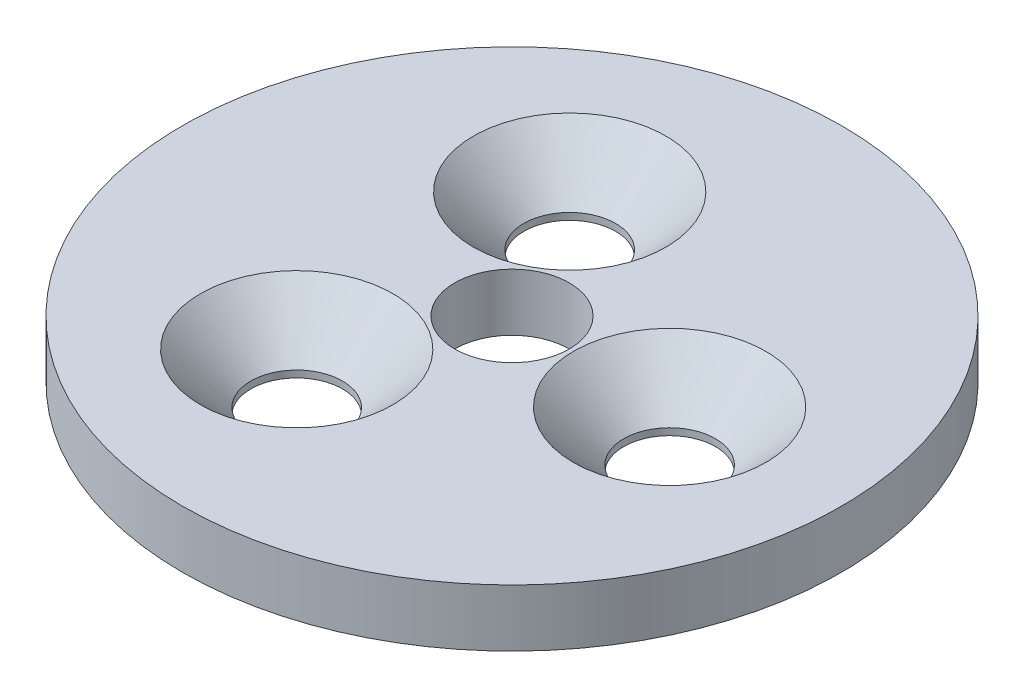
SolidWorks part; units mm, degrees
ref_plane "Ebene vorne" through (0, 0, 0) normal (0, 0, 1) x (1, 0, 0)
ref_plane "Ebene oben" through (0, 0, 0) normal (0, 1, 0) x (1, 0, 0)
ref_plane "Ebene rechts" through (0, 0, 0) normal (1, 0, 0) x (0, 0, -1)
sketch "Skizze1" plane through (0, 0, 0) normal (0, 1, 0) x (1, 0, 0)
  circle A0 centre (0, 0) radius 11.5
  dimension "D1" = 23
extrude "Aufsatz-Linear austragen1" add sketch "Skizze1" along normal blind 2
hole_wizard "Formsenkung für M3 Senkschraube mit Innensechskant1" positions "Skizze3" profile "Skizze2" countersink size "M3" standard "ISO" end condition up to next
sketch "Skizze3" plane through (0, 2, 0) normal (0, 1, 0) x (1, 0, 0)
  line L0 (0, 0) -> (9.3434, 0) construction
  point P0 (5.5, 0)
  dimension "D1" = 5.5
sketch "Skizze2" plane through (5.5, 2, 0) normal (1, 0, 0) x (0, 0, 1)
  line L0 (0, 0) -> (0, 2.001)
  line L1 (0, 2.001) -> (1.6, 2.001)
  line L2 (1.6, 2.001) -> (1.6, 1.76)
  line L3 (1.6, 1.76) -> (3.36, 0)
  line L5 (3.36, 0) -> (0, 0)
  line L6 (-1.6, 1.76) -> (-3.36, 0) construction
  line L11 (0, -6.35) -> (0, 107.95) construction
  dimension "Bohrerdurchmesser" = 3.2
  dimension "Bohrungstiefe" = 2.001
  dimension "Senkdurchmesser (Oben)" = 6.72
  dimension "Senkwinkel (Oben)" = 90
pattern_circular "Kreismuster1" count 3 over 360 about axis through (0, 0, 0) along (0, 1, 0) of "Formsenkung für M3 Senkschraube mit Innensechskant1"
hole_wizard "Ø4.0 (4) Durchmesser Bohrung1" positions "Skizze5" profile "Skizze4" hole size "Ø4.0" standard "ISO" end condition up to next
sketch "Skizze5" plane through (0, 2, 0) normal (0, 1, 0) x (1, 0, 0)
  point P0 (0, 0)
sketch "Skizze4" plane through (0, 2, 0) normal (1, 0, 0) x (0, 0, 1)
  line L0 (0, 0) -> (0, 2)
  line L1 (0, 2) -> (2, 2)
  line L2 (2, 2) -> (2, 0)
  line L5 (2, 0) -> (0, 0)
  line L11 (0, -6.35) -> (0, 107.95) construction
  dimension "Bohrerdurchmesser" = 4
  dimension "Bohrungstiefe" = 2
